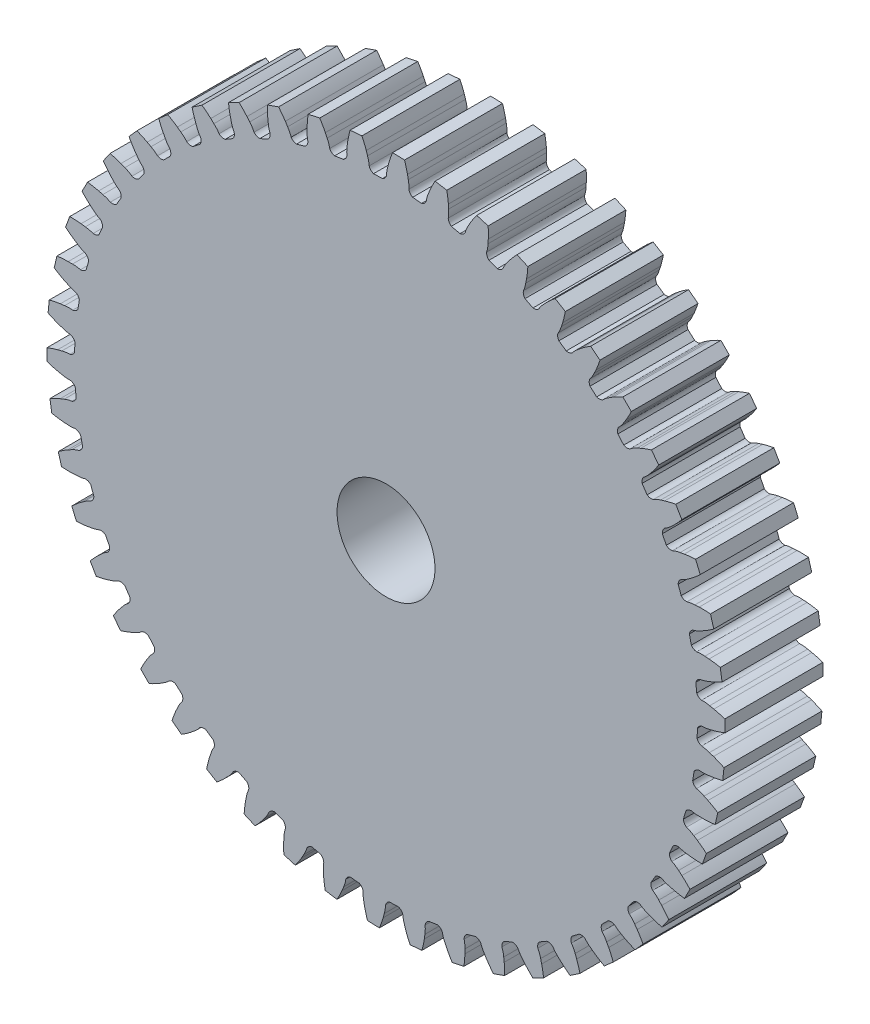
SolidWorks part; units mm, degrees
material "Alloy Steel"
ref_plane "Front Plane" through (0, 0, 0) normal (0, 0, 1) x (1, 0, 0)
ref_plane "Top Plane" through (0, 0, 0) normal (0, 1, 0) x (1, 0, 0)
ref_plane "Right Plane" through (0, 0, 0) normal (1, 0, 0) x (0, 0, -1)
ref_plane "Plane1" through (0, 0, 1.5875) normal (0, 0, 1) x (1, 0, 0)
sketch "Sketch1" plane through (0, 0, 1.5875) normal (0, 0, 1) x (1, 0, 0)
  line L0 (6.0854, 30.9194) -> (6.0622, 31.3363)
  line L1 (5.9106, 32.4269) -> (4.7682, 32.6145)
  line L2 (4.2758, 31.6296) -> (4.1205, 31.242)
  line L3 (3.4517, 30.0832) -> (2.5877, 30.1698)
  line L4 (2.1622, 31.4383) -> (2.087, 31.849)
  line L5 (1.7998, 32.912) -> (0.6429, 32.9549)
  line L6 (0.2778, 31.9161) -> (0.1724, 31.5121)
  line L7 (-0.3459, 30.2786) -> (-1.214, 30.2563)
  line L8 (-1.7951, 31.4614) -> (-1.9212, 31.8594)
  line L9 (-2.3393, 32.8781) -> (-3.4925, 32.7757)
  line L10 (-3.7245, 31.6992) -> (-3.7785, 31.2852)
  line L11 (-4.1381, 29.9965) -> (-4.9965, 29.8655)
  line L12 (-5.7241, 30.9883) -> (-5.8991, 31.3674)
  line L13 (-6.4416, 32.3256) -> (-7.5728, 32.0795)
  line L14 (-7.6681, 30.9825) -> (-7.6698, 30.5649)
  line L15 (-7.865, 29.2413) -> (-8.7003, 29.0038)
  line L16 (-9.5628, 30.0266) -> (-9.784, 30.3807)
  line L17 (-10.4423, 31.2634) -> (-11.5337, 30.8774)
  line L18 (-11.4908, 29.7771) -> (-11.4401, 29.3626)
  line L19 (-11.4679, 28.025) -> (-12.2668, 27.6847)
  line L20 (-13.2507, 28.5912) -> (-13.5145, 28.9149)
  line L21 (-14.2783, 29.7081) -> (-15.3128, 29.1884)
  line L22 (-15.1322, 28.1021) -> (-15.03, 27.6973)
  line L23 (-14.89, 26.3667) -> (-15.6399, 25.9289)
  line L24 (-16.7297, 26.705) -> (-17.032, 26.9931)
  line L25 (-17.8891, 27.6843) -> (-18.8503, 27.039)
  line L26 (-18.535, 25.9839) -> (-18.3829, 25.5951)
  line L27 (-18.0772, 24.2926) -> (-18.7663, 23.7643)
  line L28 (-19.9448, 24.3977) -> (-20.2808, 24.6455)
  line L29 (-21.2178, 25.2239) -> (-22.0905, 24.4632)
  line L30 (-21.6455, 23.456) -> (-21.4459, 23.0893)
  line L31 (-20.9793, 21.8354) -> (-21.5968, 21.2249)
  line L32 (-22.8454, 21.7055) -> (-23.2098, 21.9093)
  line L33 (-24.2119, 22.3657) -> (-24.9824, 21.5017)
  line L34 (-24.4147, 20.5581) -> (-24.1706, 20.2194)
  line L35 (-23.5506, 19.0338) -> (-24.0867, 18.3507)
  line L36 (-25.3856, 18.6711) -> (-25.7727, 18.8276)
  line L37 (-26.8242, 19.1548) -> (-27.4803, 18.201)
  line L38 (-26.7988, 17.3361) -> (-26.5142, 17.0305)
  line L39 (-25.7505, 15.932) -> (-26.1967, 15.1871)
  line L40 (-27.5256, 15.3422) -> (-27.9292, 15.449)
  line L41 (-29.0134, 15.6418) -> (-29.5448, 14.6133)
  line L42 (-28.7602, 13.8406) -> (-28.4396, 13.5731)
  line L43 (-27.5442, 12.579) -> (-27.8936, 11.7841)
  line L44 (-29.2314, 11.7714) -> (-29.6453, 11.8267)
  line L45 (-30.745, 11.8821) -> (-31.1433, 10.7951)
  line L46 (-30.2681, 10.1268) -> (-29.9165, 9.9017)
  line L47 (-28.9036, 9.0276) -> (-29.1506, 8.1951)
  line L48 (-30.4763, 8.0149) -> (-30.8938, 8.0179)
  line L49 (-31.9918, 7.935) -> (-32.2507, 6.8067)
  line L50 (-31.2987, 6.2534) -> (-30.9216, 6.0741)
  line L51 (-29.8071, 5.3339) -> (-29.9478, 4.477)
  line L52 (-31.2405, 4.132) -> (-31.6551, 4.0827)
  line L53 (-32.7341, 3.8628) -> (-32.8495, 2.7109)
  line L54 (-31.8356, 2.2813) -> (-31.4391, 2.1507)
  line L55 (-30.2406, 1.556) -> (-30.2728, 0.6882)
  line L56 (-31.512, 0.1839) -> (-31.9172, 0.083)
  line L57 (-32.9601, -0.2703) -> (-32.9303, -1.4276)
  line L58 (-31.8705, -1.7267) -> (-31.4607, -1.8066)
  line L59 (-30.1972, -2.2465) -> (-30.1203, -3.1114)
  line L60 (-31.2866, -3.767) -> (-31.6759, -3.9179)
  line L61 (-32.6663, -4.3992) -> (-32.4917, -5.5436)
  line L62 (-31.4028, -5.7076) -> (-30.9862, -5.7355)
  line L63 (-29.6775, -6.0134) -> (-29.4929, -6.8619)
  line L64 (-30.5678, -7.6586) -> (-30.9351, -7.8571)
  line L65 (-31.8574, -8.4586) -> (-31.5407, -9.5722)
  line L66 (-30.4398, -9.5984) -> (-30.023, -9.5738)
  line L67 (-28.6898, -9.6856) -> (-28.4003, -10.5043)
  line L68 (-29.3668, -11.4293) -> (-29.7064, -11.6723)
  line L69 (-30.546, -12.3847) -> (-30.0923, -13.4498)
  line L70 (-28.9968, -13.3378) -> (-28.5864, -13.2612)
  line L71 (-27.2496, -13.205) -> (-26.8598, -13.9809)
  line L72 (-27.7028, -15.0199) -> (-28.0092, -15.3034)
  line L73 (-28.7529, -16.1155) -> (-28.1693, -17.1153)
  line L74 (-27.0965, -16.8669) -> (-26.6989, -16.7395)
  line L75 (-25.3797, -16.5162) -> (-24.8957, -17.2371)
  line L76 (-25.6019, -18.3735) -> (-25.8703, -18.6933)
  line L77 (-26.5064, -19.5921) -> (-25.802, -20.5109)
  line L78 (-24.7688, -20.13) -> (-24.3903, -19.9538)
  line L79 (-23.1096, -19.5669) -> (-22.539, -20.2214)
  line L80 (-23.0972, -21.4374) -> (-23.3235, -21.7883)
  line L81 (-23.8418, -22.7598) -> (-23.0279, -23.583)
  line L82 (-22.0506, -23.0756) -> (-21.6972, -22.8533)
  line L83 (-20.475, -22.309) -> (-19.8269, -22.8869)
  line L84 (-20.2282, -24.1632) -> (-20.4088, -24.5397)
  line L85 (-20.8013, -25.5685) -> (-19.8906, -26.2832)
  line L86 (-18.9846, -25.6573) -> (-18.6618, -25.3925)
  line L87 (-17.5175, -24.6993) -> (-16.8021, -25.1914)
  line L88 (-17.0403, -26.5079) -> (-17.1722, -26.9041)
  line L89 (-17.4327, -27.974) -> (-16.4396, -28.5689)
  line L90 (-15.6191, -27.8344) -> (-15.3321, -27.5312)
  line L91 (-14.2837, -26.7) -> (-13.5123, -27.0986)
  line L92 (-13.5836, -28.4346) -> (-13.6648, -28.8442)
  line L93 (-13.7892, -29.9383) -> (-12.7293, -30.404)
  line L94 (-12.0074, -29.5725) -> (-11.7606, -29.2357)
  line L95 (-10.8247, -28.2797) -> (-10.0094, -28.5785)
  line L96 (-9.9127, -29.9129) -> (-9.9419, -30.3294)
  line L97 (-9.9282, -31.4304) -> (-8.8183, -31.7597)
  line L98 (-8.2063, -30.8443) -> (-8.0037, -30.4792)
  line L99 (-7.1949, -29.4134) -> (-6.3486, -29.6076)
  line L100 (-6.0854, -30.9194) -> (-6.0622, -31.3363)
  line L101 (-5.9106, -32.4269) -> (-4.7682, -32.6145)
  line L102 (-4.2758, -31.6296) -> (-4.1205, -31.242)
  line L103 (-3.4517, -30.0832) -> (-2.5877, -30.1698)
  line L104 (-2.1622, -31.4383) -> (-2.087, -31.849)
  line L105 (-1.7998, -32.912) -> (-0.6429, -32.9549)
  line L106 (-0.2778, -31.9161) -> (-0.1724, -31.5121)
  line L107 (0.3459, -30.2786) -> (1.214, -30.2563)
  line L108 (1.7951, -31.4614) -> (1.9212, -31.8594)
  line L109 (2.3393, -32.8781) -> (3.4925, -32.7757)
  line L110 (3.7245, -31.6992) -> (3.7785, -31.2852)
  line L111 (4.1381, -29.9965) -> (4.9965, -29.8655)
  line L112 (5.7241, -30.9883) -> (5.8991, -31.3674)
  line L113 (6.4416, -32.3256) -> (7.5728, -32.0795)
  line L114 (7.6681, -30.9825) -> (7.6698, -30.5649)
  line L115 (7.865, -29.2413) -> (8.7003, -29.0038)
  line L116 (9.5628, -30.0266) -> (9.784, -30.3807)
  line L117 (10.4423, -31.2634) -> (11.5337, -30.8774)
  line L118 (11.4908, -29.7771) -> (11.4401, -29.3626)
  line L119 (11.4679, -28.025) -> (12.2668, -27.6847)
  line L120 (13.2507, -28.5912) -> (13.5145, -28.9149)
  line L121 (14.2783, -29.7081) -> (15.3128, -29.1884)
  line L122 (15.1322, -28.1021) -> (15.03, -27.6973)
  line L123 (14.89, -26.3667) -> (15.6399, -25.9289)
  line L124 (16.7297, -26.705) -> (17.032, -26.9931)
  line L125 (17.8891, -27.6843) -> (18.8503, -27.039)
  line L126 (18.535, -25.9839) -> (18.3829, -25.5951)
  line L127 (18.0772, -24.2926) -> (18.7663, -23.7643)
  line L128 (19.9448, -24.3977) -> (20.2808, -24.6455)
  line L129 (21.2178, -25.2239) -> (22.0905, -24.4632)
  line L130 (21.6455, -23.456) -> (21.4459, -23.0893)
  line L131 (20.9793, -21.8354) -> (21.5968, -21.2249)
  line L132 (22.8454, -21.7055) -> (23.2098, -21.9093)
  line L133 (24.2119, -22.3657) -> (24.9824, -21.5017)
  line L134 (24.4147, -20.5581) -> (24.1706, -20.2194)
  line L135 (23.5506, -19.0338) -> (24.0867, -18.3507)
  line L136 (25.3856, -18.6711) -> (25.7727, -18.8276)
  line L137 (26.8242, -19.1548) -> (27.4803, -18.201)
  line L138 (26.7988, -17.3361) -> (26.5142, -17.0305)
  line L139 (25.7505, -15.932) -> (26.1967, -15.1871)
  line L140 (27.5256, -15.3422) -> (27.9292, -15.449)
  line L141 (29.0134, -15.6418) -> (29.5448, -14.6133)
  line L142 (28.7602, -13.8406) -> (28.4396, -13.5731)
  line L143 (27.5442, -12.579) -> (27.8936, -11.7841)
  line L144 (29.2314, -11.7714) -> (29.6453, -11.8267)
  line L145 (30.745, -11.8821) -> (31.1433, -10.7951)
  line L146 (30.2681, -10.1268) -> (29.9165, -9.9017)
  line L147 (28.9036, -9.0276) -> (29.1506, -8.1951)
  line L148 (30.4763, -8.0149) -> (30.8938, -8.0179)
  line L149 (31.9918, -7.935) -> (32.2507, -6.8067)
  line L150 (31.2987, -6.2534) -> (30.9216, -6.0741)
  line L151 (29.8071, -5.3339) -> (29.9478, -4.477)
  line L152 (31.2405, -4.132) -> (31.6551, -4.0827)
  line L153 (32.7341, -3.8628) -> (32.8495, -2.7109)
  line L154 (31.8356, -2.2813) -> (31.4391, -2.1507)
  line L155 (30.2406, -1.556) -> (30.2728, -0.6882)
  line L156 (31.512, -0.1839) -> (31.9172, -0.083)
  line L157 (32.9601, 0.2703) -> (32.9303, 1.4276)
  line L158 (31.8705, 1.7267) -> (31.4607, 1.8066)
  line L159 (30.1972, 2.2465) -> (30.1203, 3.1114)
  line L160 (31.2866, 3.767) -> (31.6759, 3.9179)
  line L161 (32.6663, 4.3992) -> (32.4917, 5.5436)
  line L162 (31.4028, 5.7076) -> (30.9862, 5.7355)
  line L163 (29.6775, 6.0134) -> (29.4929, 6.8619)
  line L164 (30.5678, 7.6586) -> (30.9351, 7.8571)
  line L165 (31.8574, 8.4586) -> (31.5407, 9.5722)
  line L166 (30.4398, 9.5984) -> (30.023, 9.5738)
  line L167 (28.6898, 9.6856) -> (28.4003, 10.5043)
  line L168 (29.3668, 11.4293) -> (29.7064, 11.6723)
  line L169 (30.546, 12.3847) -> (30.0923, 13.4498)
  line L170 (28.9968, 13.3378) -> (28.5864, 13.2612)
  line L171 (27.2496, 13.205) -> (26.8598, 13.9809)
  line L172 (27.7028, 15.0199) -> (28.0092, 15.3034)
  line L173 (28.7529, 16.1155) -> (28.1693, 17.1153)
  line L174 (27.0965, 16.8669) -> (26.6989, 16.7395)
  line L175 (25.3797, 16.5162) -> (24.8957, 17.2371)
  line L176 (25.6019, 18.3735) -> (25.8703, 18.6933)
  line L177 (26.5064, 19.5921) -> (25.802, 20.5109)
  line L178 (24.7688, 20.13) -> (24.3903, 19.9538)
  line L179 (23.1096, 19.5669) -> (22.539, 20.2214)
  line L180 (23.0972, 21.4374) -> (23.3235, 21.7883)
  line L181 (23.8418, 22.7598) -> (23.0279, 23.583)
  line L182 (22.0506, 23.0756) -> (21.6972, 22.8533)
  line L183 (20.475, 22.309) -> (19.8269, 22.8869)
  line L184 (20.2282, 24.1632) -> (20.4088, 24.5397)
  line L185 (20.8013, 25.5685) -> (19.8906, 26.2832)
  line L186 (18.9846, 25.6573) -> (18.6618, 25.3925)
  line L187 (17.5175, 24.6993) -> (16.8021, 25.1914)
  line L188 (17.0403, 26.5079) -> (17.1722, 26.9041)
  line L189 (17.4327, 27.974) -> (16.4396, 28.5689)
  line L190 (15.6191, 27.8344) -> (15.3321, 27.5312)
  line L191 (14.2837, 26.7) -> (13.5123, 27.0986)
  line L192 (13.5836, 28.4346) -> (13.6648, 28.8442)
  line L193 (13.7892, 29.9383) -> (12.7293, 30.404)
  line L194 (12.0074, 29.5725) -> (11.7606, 29.2357)
  line L195 (10.8247, 28.2797) -> (10.0094, 28.5785)
  line L196 (9.9127, 29.9129) -> (9.9419, 30.3294)
  line L197 (9.9282, 31.4304) -> (8.8183, 31.7597)
  line L198 (8.2063, 30.8443) -> (8.0037, 30.4792)
  line L199 (7.1949, 29.4134) -> (6.3486, 29.6076)
  circle A0 centre (0, 0) radius 4.7625
  arc A1 (6.3486, 29.6076) -> (6.0483, 30.1378) centre (6.7187, 30.1674) cw
  arc A2 (6.0483, 30.1378) -> (6.0854, 30.9194) centre (3.3661, 30.657) ccw
  arc A3 (6.0622, 31.3363) -> (5.9106, 32.4269) centre (-4.1695, 30.4695) ccw
  arc A4 (4.7682, 32.6145) -> (4.2758, 31.6296) centre (13.6932, 27.5367) ccw
  arc A5 (4.1205, 31.242) -> (3.9058, 30.4895) centre (6.6132, 30.1239) ccw
  arc A6 (3.9058, 30.4895) -> (3.4517, 30.0832) centre (3.2801, 30.732) cw
  arc A7 (2.5877, 30.1698) -> (2.2233, 30.6582) centre (2.8847, 30.7716) cw
  arc A8 (2.2233, 30.6582) -> (2.1622, 31.4383) centre (-0.5028, 30.8371) ccw
  arc A9 (2.087, 31.849) -> (1.7998, 32.912) centre (-7.9554, 29.7067) ccw
  arc A10 (0.6429, 32.9549) -> (0.2778, 31.9161) centre (10.1339, 29.0358) ccw
  arc A11 (0.1724, 31.5121) -> (0.0536, 30.7386) centre (2.7856, 30.7152) ccw
  arc A12 (0.0536, 30.7386) -> (-0.3459, 30.2786) centre (-0.5975, 30.9007) cw
  arc A13 (-1.214, 30.2563) -> (-1.6367, 30.6951) centre (-0.9947, 30.8905) cw
  arc A14 (-1.6367, 30.6951) -> (-1.7951, 31.4614) centre (-4.3638, 30.531) ccw
  arc A15 (-1.9212, 31.8594) -> (-2.3393, 32.8781) centre (-11.6159, 28.4753) ccw
  arc A16 (-3.4925, 32.7757) -> (-3.7245, 31.6992) centre (6.4149, 30.077) ccw
  arc A17 (-3.7785, 31.2852) -> (-3.7993, 30.503) centre (-1.086, 30.8221) ccw
  arc A18 (-3.7993, 30.503) -> (-4.1381, 29.9965) centre (-4.4657, 30.5822) cw
  arc A19 (-4.9965, 29.8655) -> (-5.4709, 30.2479) centre (-4.8585, 30.5223) cw
  arc A20 (-5.4709, 30.2479) -> (-5.7241, 30.9883) centre (-8.1559, 29.7433) ccw
  arc A21 (-5.8991, 31.3674) -> (-6.4416, 32.3256) centre (-15.0932, 26.7949) ccw
  arc A22 (-7.5728, 32.0795) -> (-7.6681, 30.9825) centre (2.5947, 30.6438) ccw
  arc A23 (-7.6698, 30.5649) -> (-7.5924, 29.7863) centre (-4.9405, 30.4429) ccw
  arc A24 (-7.5924, 29.7863) -> (-7.865, 29.2413) centre (-8.2635, 29.7813) cw
  arc A25 (-8.7003, 29.0038) -> (-9.2188, 29.3237) centre (-8.6456, 29.6726) cw
  arc A26 (-9.2188, 29.3237) -> (-9.5628, 30.0266) centre (-11.8194, 28.4865) ccw
  arc A27 (-9.784, 30.3807) -> (-10.4423, 31.2634) centre (-18.3325, 24.692) ccw
  arc A28 (-11.5337, 30.8774) -> (-11.4908, 29.7771) centre (-1.2665, 30.7274) ccw
  arc A29 (-11.4401, 29.3626) -> (-11.2658, 28.5998) centre (-8.7171, 29.5837) ccw
  arc A30 (-11.2658, 28.5998) -> (-11.4679, 28.025) centre (-11.9309, 28.5108) cw
  arc A31 (-12.2668, 27.6847) -> (-12.8214, 27.9371) centre (-12.2964, 28.3551) cw
  arc A32 (-12.8214, 27.9371) -> (-13.2507, 28.5912) centre (-15.2965, 26.7805) ccw
  arc A33 (-13.5145, 28.9149) -> (-14.2783, 29.7081) centre (-21.2827, 22.1996) ccw
  arc A34 (-15.3128, 29.1884) -> (-15.1322, 28.1021) centre (-5.1077, 30.3263) ccw
  arc A35 (-15.03, 27.6973) -> (-14.7614, 26.9623) centre (-12.3561, 28.2579) ccw
  arc A36 (-14.7614, 26.9623) -> (-14.89, 26.3667) centre (-15.4102, 26.7907) cw
  arc A37 (-15.6399, 25.9289) -> (-16.2217, 26.1098) centre (-15.7533, 26.5903) cw
  arc A38 (-16.2217, 26.1098) -> (-16.7297, 26.705) centre (-18.5324, 24.6522) ccw
  arc A39 (-17.032, 26.9931) -> (-17.8891, 27.6843) centre (-23.8972, 19.3571) ccw
  arc A40 (-18.8503, 27.039) -> (-18.535, 25.9839) centre (-8.8683, 29.447) ccw
  arc A41 (-18.3829, 25.5951) -> (-18.0243, 24.8996) centre (-15.8004, 26.4864) ccw
  arc A42 (-18.0243, 24.8996) -> (-18.0772, 24.2926) centre (-18.6464, 24.648) cw
  arc A43 (-18.7663, 23.7643) -> (-19.3662, 23.8708) centre (-18.9617, 24.4063) cw
  arc A44 (-19.3662, 23.8708) -> (-19.9448, 24.3977) centre (-21.476, 22.1351) ccw
  arc A45 (-20.2808, 24.6455) -> (-21.2178, 25.2239) centre (-26.1349, 16.2094) ccw
  arc A46 (-22.0905, 24.4632) -> (-21.6455, 23.456) centre (-12.489, 28.1033) ccw
  arc A47 (-21.4459, 23.0893) -> (-21.0029, 22.4442) centre (-18.9954, 24.2972) ccw
  arc A48 (-21.0029, 22.4442) -> (-20.9793, 21.8354) centre (-21.5886, 22.1166) cw
  arc A49 (-21.5968, 21.2249) -> (-22.2053, 21.2554) centre (-21.8711, 21.8373) cw
  arc A50 (-22.2053, 21.2554) -> (-22.8454, 21.7055) centre (-24.0809, 19.2689) ccw
  arc A51 (-23.2098, 21.9093) -> (-24.2119, 22.3657) centre (-27.9603, 12.806) ccw
  arc A52 (-24.9824, 21.5017) -> (-24.4147, 20.5581) centre (-15.9128, 26.3165) ccw
  arc A53 (-24.1706, 20.2194) -> (-23.6503, 19.6349) centre (-21.8909, 21.7249) ccw
  arc A54 (-23.6503, 19.6349) -> (-23.5506, 19.0338) centre (-24.1903, 19.2365) cw
  arc A55 (-24.0867, 18.3507) -> (-24.6942, 18.3047) centre (-24.4356, 18.9239) cw
  arc A56 (-24.6942, 18.3047) -> (-25.3856, 18.6711) centre (-26.3061, 16.0988) ccw
  arc A57 (-25.7727, 18.8276) -> (-26.8242, 19.1548) centre (-29.3449, 9.2006) ccw
  arc A58 (-27.4803, 18.201) -> (-26.7988, 17.3361) centre (-19.0857, 24.1145) ccw
  arc A59 (-26.5142, 17.0305) -> (-25.9247, 16.5159) centre (-24.4411, 18.8099) ccw
  arc A60 (-25.9247, 16.5159) -> (-25.7505, 15.932) centre (-26.4105, 16.0529) cw
  arc A61 (-26.1967, 15.1871) -> (-26.7937, 15.0653) centre (-26.6147, 15.7121) cw
  arc A62 (-26.7937, 15.0653) -> (-27.5256, 15.3422) centre (-28.1164, 12.6748) ccw
  arc A63 (-27.9292, 15.449) -> (-29.0134, 15.6418) centre (-30.2666, 5.4502) ccw
  arc A64 (-29.5448, 14.6133) -> (-28.7602, 13.8406) centre (-21.9575, 21.5323) ccw
  arc A65 (-28.4396, 13.5731) -> (-27.7903, 13.1364) centre (-26.6059, 15.5983) ccw
  arc A66 (-27.7903, 13.1364) -> (-27.5442, 12.579) centre (-28.2142, 12.6162) cw
  arc A67 (-27.8936, 11.7841) -> (-28.4706, 11.5884) centre (-28.3741, 12.2525) cw
  arc A68 (-28.4706, 11.5884) -> (-29.2314, 11.7714) centre (-29.4832, 9.051) ccw
  arc A69 (-29.6453, 11.8267) -> (-30.745, 11.8821) centre (-30.7111, 1.6138) ccw
  arc A70 (-31.1433, 10.7951) -> (-30.2681, 10.1268) centre (-24.4831, 18.6105) ccw
  arc A71 (-29.9165, 9.9017) -> (-29.2176, 9.5498) centre (-28.3511, 12.1407) ccw
  arc A72 (-29.2176, 9.5498) -> (-28.9036, 9.0276) centre (-29.573, 8.9806) cw
  arc A73 (-29.1506, 8.1951) -> (-29.6985, 7.9287) centre (-29.686, 8.5997) cw
  arc A74 (-29.6985, 7.9287) -> (-30.4763, 8.0149) centre (-30.3851, 5.2844) ccw
  arc A75 (-30.8938, 8.0179) -> (-31.9918, 7.935) centre (-30.6712, -2.248) ccw
  arc A76 (-32.2507, 6.8067) -> (-31.2987, 6.2534) centre (-26.6226, 15.3952) ccw
  arc A77 (-30.9216, 6.0741) -> (-30.1841, 5.8125) centre (-29.6492, 8.4917) ccw
  arc A78 (-30.1841, 5.8125) -> (-29.8071, 5.3339) centre (-30.4654, 5.2033) cw
  arc A79 (-29.9478, 4.477) -> (-30.4581, 4.144) centre (-30.5297, 4.8112) cw
  arc A80 (-30.4581, 4.144) -> (-31.2405, 4.132) centre (-30.8079, 1.4344) ccw
  arc A81 (-31.6551, 4.0827) -> (-32.7341, 3.8628) centre (-30.1476, -6.0744) ccw
  arc A82 (-32.8495, 2.7109) -> (-31.8356, 2.2813) centre (-28.3422, 11.9371) ccw
  arc A83 (-31.4391, 2.1507) -> (-30.6746, 1.9836) centre (-30.4797, 4.7087) ccw
  arc A84 (-30.6746, 1.9836) -> (-30.2406, 1.556) centre (-30.8773, 1.3439) cw
  arc A85 (-30.2728, 0.6882) -> (-30.7373, 0.2939) centre (-30.892, 0.9469) cw
  arc A86 (-30.7373, 0.2939) -> (-31.512, 0.1839) centre (-30.7447, -2.4381) ccw
  arc A87 (-31.9172, 0.083) -> (-32.9601, -0.2703) centre (-29.1485, -9.805) ccw
  arc A88 (-32.9303, -1.4276) -> (-31.8705, -1.7267) centre (-29.6148, 8.2908) ccw
  arc A89 (-31.4607, -1.8066) -> (-30.6814, -1.8766) centre (-30.8295, 0.8514) ccw
  arc A90 (-30.6814, -1.8766) -> (-30.1972, -2.2465) centre (-30.8022, -2.5366) cw
  arc A91 (-30.1203, -3.1114) -> (-30.5317, -3.5608) centre (-30.7671, -2.9324) cw
  arc A92 (-30.5317, -3.5608) -> (-31.2866, -3.767) centre (-30.1967, -6.2722) ccw
  arc A93 (-31.6759, -3.9179) -> (-32.6663, -4.3992) centre (-27.6898, -13.381) ccw
  arc A94 (-32.4917, -5.5436) -> (-31.4028, -5.7076) centre (-30.4204, 4.5137) ccw
  arc A95 (-30.9862, -5.7355) -> (-30.2042, -5.7071) centre (-30.6931, -3.0192) ccw
  arc A96 (-30.2042, -5.7071) -> (-29.6775, -6.0134) centre (-30.2414, -6.3772) cw
  arc A97 (-29.4929, -6.8619) -> (-29.8447, -7.3594) centre (-30.157, -6.7654) cw
  arc A98 (-29.8447, -7.3594) -> (-30.5678, -7.6586) centre (-29.1725, -10.0074) ccw
  arc A99 (-30.9351, -7.8571) -> (-31.8574, -8.4586) centre (-25.7944, -16.7459) ccw
  arc A100 (-31.5407, -9.5722) -> (-30.4398, -9.5984) centre (-30.7462, 0.6654) ccw
  arc A101 (-30.023, -9.5738) -> (-29.2508, -9.4477) centre (-30.0727, -6.8423) ccw
  arc A102 (-29.2508, -9.4477) -> (-28.6898, -9.6856) centre (-29.2037, -10.1172) cw
  arc A103 (-28.4003, -10.5043) -> (-28.687, -11.0419) centre (-29.0712, -10.4917) cw
  arc A104 (-28.687, -11.0419) -> (-29.3668, -11.4293) centre (-27.6882, -13.5848) ccw
  arc A105 (-29.7064, -11.6723) -> (-30.546, -12.3847) centre (-23.4921, -19.8468) ccw
  arc A106 (-30.0923, -13.4498) -> (-28.9968, -13.3378) centre (-30.5872, -3.1934) ccw
  arc A107 (-28.5864, -13.2612) -> (-27.836, -13.0393) centre (-28.978, -10.5574) ccw
  arc A108 (-27.836, -13.0393) -> (-27.2496, -13.205) centre (-27.7054, -13.6976) cw
  arc A109 (-26.8598, -13.9809) -> (-27.0769, -14.5503) centre (-27.527, -14.0526) cw
  arc A110 (-27.0769, -14.5503) -> (-27.7028, -15.0199) centre (-25.7672, -16.9479) ccw
  arc A111 (-28.0092, -15.3034) -> (-28.7529, -16.1155) centre (-20.8194, -22.6346) ccw
  arc A112 (-28.1693, -17.1153) -> (-27.0965, -16.8669) centre (-29.9458, -7.0018) ccw
  arc A113 (-26.6989, -16.7395) -> (-25.9822, -16.4253) centre (-27.4263, -14.1061) ccw
  arc A114 (-25.9822, -16.4253) -> (-25.3797, -16.5162) centre (-25.7702, -17.062) cw
  arc A115 (-24.8957, -17.2371) -> (-25.0397, -17.8292) centre (-25.5487, -17.3918) cw
  arc A116 (-25.0397, -17.8292) -> (-25.6019, -18.3735) centre (-23.4399, -20.0438) ccw
  arc A117 (-25.8703, -18.6933) -> (-26.5064, -19.5921) centre (-17.8184, -25.0655) ccw
  arc A118 (-25.802, -20.5109) -> (-24.7688, -20.13) centre (-28.8321, -10.6998) ccw
  arc A119 (-24.3903, -19.9538) -> (-23.7187, -19.5522) centre (-25.442, -17.4323) ccw
  arc A120 (-23.7187, -19.5522) -> (-23.1096, -19.5669) centre (-23.4285, -20.1573) cw
  arc A121 (-22.539, -20.2214) -> (-22.6077, -20.8269) centre (-23.1675, -20.4568) cw
  arc A122 (-22.6077, -20.8269) -> (-23.0972, -21.4374) centre (-20.7429, -22.8235) ccw
  arc A123 (-23.3235, -21.7883) -> (-23.8418, -22.7598) centre (-14.5364, -27.1011) ccw
  arc A124 (-23.0279, -23.583) -> (-22.0506, -23.0756) centre (-27.2637, -14.229) ccw
  arc A125 (-21.6972, -22.8533) -> (-21.0812, -22.3708) centre (-23.0566, -20.4836) ccw
  arc A126 (-21.0812, -22.3708) -> (-20.475, -22.309) centre (-20.7174, -22.9347) cw
  arc A127 (-19.8269, -22.8869) -> (-19.8191, -23.4962) centre (-20.4209, -23.1991) cw
  arc A128 (-19.8191, -23.4962) -> (-20.2282, -24.1632) centre (-17.7188, -25.2433) ccw
  arc A129 (-20.4088, -24.5397) -> (-20.8013, -25.5685) centre (-11.0251, -28.7093) ccw
  arc A130 (-19.8906, -26.2832) -> (-18.9846, -25.6573) centre (-25.2653, -17.5339) ccw
  arc A131 (-18.6618, -25.3925) -> (-18.1111, -24.8365) centre (-20.3075, -23.2118) ccw
  arc A132 (-18.1111, -24.8365) -> (-17.5175, -24.6993) centre (-17.6796, -25.3505) cw
  arc A133 (-16.8021, -25.1914) -> (-16.718, -25.7949) centre (-17.3522, -25.5756) cw
  arc A134 (-16.718, -25.7949) -> (-17.0403, -26.5079) centre (-14.4153, -27.265) ccw
  arc A135 (-17.1722, -26.9041) -> (-17.4327, -27.974) centre (-7.3399, -29.8647) ccw
  arc A136 (-16.4396, -28.5689) -> (-15.6191, -27.8344) centre (-22.8685, -20.5622) ccw
  arc A137 (-15.3321, -27.5312) -> (-14.8555, -26.9106) centre (-17.2382, -25.574) ccw
  arc A138 (-14.8555, -26.9106) -> (-14.2837, -26.7) centre (-14.3629, -27.3664) cw
  arc A139 (-13.5123, -27.0986) -> (-13.3532, -27.6868) centre (-14.0099, -27.5488) cw
  arc A140 (-13.3532, -27.6868) -> (-13.5836, -28.4346) centre (-10.8844, -28.8567) ccw
  arc A141 (-13.6648, -28.8442) -> (-13.7892, -29.9383) centre (-3.539, -30.5491) ccw
  arc A142 (-12.7293, -30.404) -> (-12.0074, -29.5725) centre (-20.1111, -23.2662) ccw
  arc A143 (-11.7606, -29.2357) -> (-11.3655, -28.5603) centre (-13.897, -27.5328) ccw
  arc A144 (-11.3655, -28.5603) -> (-10.8247, -28.2797) centre (-10.8197, -28.9508) cw
  arc A145 (-10.0094, -28.5785) -> (-9.7778, -29.1421) centre (-10.4467, -29.0874) cw
  arc A146 (-9.7778, -29.1421) -> (-9.9127, -29.9129) centre (-7.1819, -29.9934) ccw
  arc A147 (-9.9419, -30.3294) -> (-9.9282, -31.4304) centre (0.3177, -30.7518) ccw
  arc A148 (-8.8183, -31.7597) -> (-8.2063, -30.8443) centre (-17.0365, -25.6034) ccw
  arc A149 (-8.0037, -30.4792) -> (-7.6964, -29.7596) centre (-10.3366, -29.0575) ccw
  arc A150 (-7.6964, -29.7596) -> (-7.1949, -29.4134) centre (-7.1059, -30.0785) cw
  arc A151 (-6.3486, -29.6076) -> (-6.0483, -30.1378) centre (-6.7187, -30.1674) cw
  arc A152 (-6.0483, -30.1378) -> (-6.0854, -30.9194) centre (-3.3661, -30.657) ccw
  arc A153 (-6.0622, -31.3363) -> (-5.9106, -32.4269) centre (4.1695, -30.4695) ccw
  arc A154 (-4.7682, -32.6145) -> (-4.2758, -31.6296) centre (-13.6932, -27.5367) ccw
  arc A155 (-4.1205, -31.242) -> (-3.9058, -30.4895) centre (-6.6132, -30.1239) ccw
  arc A156 (-3.9058, -30.4895) -> (-3.4517, -30.0832) centre (-3.2801, -30.732) cw
  arc A157 (-2.5877, -30.1698) -> (-2.2233, -30.6582) centre (-2.8847, -30.7716) cw
  arc A158 (-2.2233, -30.6582) -> (-2.1622, -31.4383) centre (0.5028, -30.8371) ccw
  arc A159 (-2.087, -31.849) -> (-1.7998, -32.912) centre (7.9554, -29.7067) ccw
  arc A160 (-0.6429, -32.9549) -> (-0.2778, -31.9161) centre (-10.1339, -29.0358) ccw
  arc A161 (-0.1724, -31.5121) -> (-0.0536, -30.7386) centre (-2.7856, -30.7152) ccw
  arc A162 (-0.0536, -30.7386) -> (0.3459, -30.2786) centre (0.5975, -30.9007) cw
  arc A163 (1.214, -30.2563) -> (1.6367, -30.6951) centre (0.9947, -30.8905) cw
  arc A164 (1.6367, -30.6951) -> (1.7951, -31.4614) centre (4.3638, -30.531) ccw
  arc A165 (1.9212, -31.8594) -> (2.3393, -32.8781) centre (11.6159, -28.4753) ccw
  arc A166 (3.4925, -32.7757) -> (3.7245, -31.6992) centre (-6.4149, -30.077) ccw
  arc A167 (3.7785, -31.2852) -> (3.7993, -30.503) centre (1.086, -30.8221) ccw
  arc A168 (3.7993, -30.503) -> (4.1381, -29.9965) centre (4.4657, -30.5822) cw
  arc A169 (4.9965, -29.8655) -> (5.4709, -30.2479) centre (4.8585, -30.5223) cw
  arc A170 (5.4709, -30.2479) -> (5.7241, -30.9883) centre (8.1559, -29.7433) ccw
  arc A171 (5.8991, -31.3674) -> (6.4416, -32.3256) centre (15.0932, -26.7949) ccw
  arc A172 (7.5728, -32.0795) -> (7.6681, -30.9825) centre (-2.5947, -30.6438) ccw
  arc A173 (7.6698, -30.5649) -> (7.5924, -29.7863) centre (4.9405, -30.4429) ccw
  arc A174 (7.5924, -29.7863) -> (7.865, -29.2413) centre (8.2635, -29.7813) cw
  arc A175 (8.7003, -29.0038) -> (9.2188, -29.3237) centre (8.6456, -29.6726) cw
  arc A176 (9.2188, -29.3237) -> (9.5628, -30.0266) centre (11.8194, -28.4865) ccw
  arc A177 (9.784, -30.3807) -> (10.4423, -31.2634) centre (18.3325, -24.692) ccw
  arc A178 (11.5337, -30.8774) -> (11.4908, -29.7771) centre (1.2665, -30.7274) ccw
  arc A179 (11.4401, -29.3626) -> (11.2658, -28.5998) centre (8.7171, -29.5837) ccw
  arc A180 (11.2658, -28.5998) -> (11.4679, -28.025) centre (11.9309, -28.5108) cw
  arc A181 (12.2668, -27.6847) -> (12.8214, -27.9371) centre (12.2964, -28.3551) cw
  arc A182 (12.8214, -27.9371) -> (13.2507, -28.5912) centre (15.2965, -26.7805) ccw
  arc A183 (13.5145, -28.9149) -> (14.2783, -29.7081) centre (21.2827, -22.1996) ccw
  arc A184 (15.3128, -29.1884) -> (15.1322, -28.1021) centre (5.1077, -30.3263) ccw
  arc A185 (15.03, -27.6973) -> (14.7614, -26.9623) centre (12.3561, -28.2579) ccw
  arc A186 (14.7614, -26.9623) -> (14.89, -26.3667) centre (15.4102, -26.7907) cw
  arc A187 (15.6399, -25.9289) -> (16.2217, -26.1098) centre (15.7533, -26.5903) cw
  arc A188 (16.2217, -26.1098) -> (16.7297, -26.705) centre (18.5324, -24.6522) ccw
  arc A189 (17.032, -26.9931) -> (17.8891, -27.6843) centre (23.8972, -19.3571) ccw
  arc A190 (18.8503, -27.039) -> (18.535, -25.9839) centre (8.8683, -29.447) ccw
  arc A191 (18.3829, -25.5951) -> (18.0243, -24.8996) centre (15.8004, -26.4864) ccw
  arc A192 (18.0243, -24.8996) -> (18.0772, -24.2926) centre (18.6464, -24.648) cw
  arc A193 (18.7663, -23.7643) -> (19.3662, -23.8708) centre (18.9617, -24.4063) cw
  arc A194 (19.3662, -23.8708) -> (19.9448, -24.3977) centre (21.476, -22.1351) ccw
  arc A195 (20.2808, -24.6455) -> (21.2178, -25.2239) centre (26.1349, -16.2094) ccw
  arc A196 (22.0905, -24.4632) -> (21.6455, -23.456) centre (12.489, -28.1033) ccw
  arc A197 (21.4459, -23.0893) -> (21.0029, -22.4442) centre (18.9954, -24.2972) ccw
  arc A198 (21.0029, -22.4442) -> (20.9793, -21.8354) centre (21.5886, -22.1166) cw
  arc A199 (21.5968, -21.2249) -> (22.2053, -21.2554) centre (21.8711, -21.8373) cw
  arc A200 (22.2053, -21.2554) -> (22.8454, -21.7055) centre (24.0809, -19.2689) ccw
  arc A201 (23.2098, -21.9093) -> (24.2119, -22.3657) centre (27.9603, -12.806) ccw
  arc A202 (24.9824, -21.5017) -> (24.4147, -20.5581) centre (15.9128, -26.3165) ccw
  arc A203 (24.1706, -20.2194) -> (23.6503, -19.6349) centre (21.8909, -21.7249) ccw
  arc A204 (23.6503, -19.6349) -> (23.5506, -19.0338) centre (24.1903, -19.2365) cw
  arc A205 (24.0867, -18.3507) -> (24.6942, -18.3047) centre (24.4356, -18.9239) cw
  arc A206 (24.6942, -18.3047) -> (25.3856, -18.6711) centre (26.3061, -16.0988) ccw
  arc A207 (25.7727, -18.8276) -> (26.8242, -19.1548) centre (29.3449, -9.2006) ccw
  arc A208 (27.4803, -18.201) -> (26.7988, -17.3361) centre (19.0857, -24.1145) ccw
  arc A209 (26.5142, -17.0305) -> (25.9247, -16.5159) centre (24.4411, -18.8099) ccw
  arc A210 (25.9247, -16.5159) -> (25.7505, -15.932) centre (26.4105, -16.0529) cw
  arc A211 (26.1967, -15.1871) -> (26.7937, -15.0653) centre (26.6147, -15.7121) cw
  arc A212 (26.7937, -15.0653) -> (27.5256, -15.3422) centre (28.1164, -12.6748) ccw
  arc A213 (27.9292, -15.449) -> (29.0134, -15.6418) centre (30.2666, -5.4502) ccw
  arc A214 (29.5448, -14.6133) -> (28.7602, -13.8406) centre (21.9575, -21.5323) ccw
  arc A215 (28.4396, -13.5731) -> (27.7903, -13.1364) centre (26.6059, -15.5983) ccw
  arc A216 (27.7903, -13.1364) -> (27.5442, -12.579) centre (28.2142, -12.6162) cw
  arc A217 (27.8936, -11.7841) -> (28.4706, -11.5884) centre (28.3741, -12.2525) cw
  arc A218 (28.4706, -11.5884) -> (29.2314, -11.7714) centre (29.4832, -9.051) ccw
  arc A219 (29.6453, -11.8267) -> (30.745, -11.8821) centre (30.7111, -1.6138) ccw
  arc A220 (31.1433, -10.7951) -> (30.2681, -10.1268) centre (24.4831, -18.6105) ccw
  arc A221 (29.9165, -9.9017) -> (29.2176, -9.5498) centre (28.3511, -12.1407) ccw
  arc A222 (29.2176, -9.5498) -> (28.9036, -9.0276) centre (29.573, -8.9806) cw
  arc A223 (29.1506, -8.1951) -> (29.6985, -7.9287) centre (29.686, -8.5997) cw
  arc A224 (29.6985, -7.9287) -> (30.4763, -8.0149) centre (30.3851, -5.2844) ccw
  arc A225 (30.8938, -8.0179) -> (31.9918, -7.935) centre (30.6712, 2.248) ccw
  arc A226 (32.2507, -6.8067) -> (31.2987, -6.2534) centre (26.6226, -15.3952) ccw
  arc A227 (30.9216, -6.0741) -> (30.1841, -5.8125) centre (29.6492, -8.4917) ccw
  arc A228 (30.1841, -5.8125) -> (29.8071, -5.3339) centre (30.4654, -5.2033) cw
  arc A229 (29.9478, -4.477) -> (30.4581, -4.144) centre (30.5297, -4.8112) cw
  arc A230 (30.4581, -4.144) -> (31.2405, -4.132) centre (30.8079, -1.4344) ccw
  arc A231 (31.6551, -4.0827) -> (32.7341, -3.8628) centre (30.1476, 6.0744) ccw
  arc A232 (32.8495, -2.7109) -> (31.8356, -2.2813) centre (28.3422, -11.9371) ccw
  arc A233 (31.4391, -2.1507) -> (30.6746, -1.9836) centre (30.4797, -4.7087) ccw
  arc A234 (30.6746, -1.9836) -> (30.2406, -1.556) centre (30.8773, -1.3439) cw
  arc A235 (30.2728, -0.6882) -> (30.7373, -0.2939) centre (30.892, -0.9469) cw
  arc A236 (30.7373, -0.2939) -> (31.512, -0.1839) centre (30.7447, 2.4381) ccw
  arc A237 (31.9172, -0.083) -> (32.9601, 0.2703) centre (29.1485, 9.805) ccw
  arc A238 (32.9303, 1.4276) -> (31.8705, 1.7267) centre (29.6148, -8.2908) ccw
  arc A239 (31.4607, 1.8066) -> (30.6814, 1.8766) centre (30.8295, -0.8514) ccw
  arc A240 (30.6814, 1.8766) -> (30.1972, 2.2465) centre (30.8022, 2.5366) cw
  arc A241 (30.1203, 3.1114) -> (30.5317, 3.5608) centre (30.7671, 2.9324) cw
  arc A242 (30.5317, 3.5608) -> (31.2866, 3.767) centre (30.1967, 6.2722) ccw
  arc A243 (31.6759, 3.9179) -> (32.6663, 4.3992) centre (27.6898, 13.381) ccw
  arc A244 (32.4917, 5.5436) -> (31.4028, 5.7076) centre (30.4204, -4.5137) ccw
  arc A245 (30.9862, 5.7355) -> (30.2042, 5.7071) centre (30.6931, 3.0192) ccw
  arc A246 (30.2042, 5.7071) -> (29.6775, 6.0134) centre (30.2414, 6.3772) cw
  arc A247 (29.4929, 6.8619) -> (29.8447, 7.3594) centre (30.157, 6.7654) cw
  arc A248 (29.8447, 7.3594) -> (30.5678, 7.6586) centre (29.1725, 10.0074) ccw
  arc A249 (30.9351, 7.8571) -> (31.8574, 8.4586) centre (25.7944, 16.7459) ccw
  arc A250 (31.5407, 9.5722) -> (30.4398, 9.5984) centre (30.7462, -0.6654) ccw
  arc A251 (30.023, 9.5738) -> (29.2508, 9.4477) centre (30.0727, 6.8423) ccw
  arc A252 (29.2508, 9.4477) -> (28.6898, 9.6856) centre (29.2037, 10.1172) cw
  arc A253 (28.4003, 10.5043) -> (28.687, 11.0419) centre (29.0712, 10.4917) cw
  arc A254 (28.687, 11.0419) -> (29.3668, 11.4293) centre (27.6882, 13.5848) ccw
  arc A255 (29.7064, 11.6723) -> (30.546, 12.3847) centre (23.4921, 19.8468) ccw
  arc A256 (30.0923, 13.4498) -> (28.9968, 13.3378) centre (30.5872, 3.1934) ccw
  arc A257 (28.5864, 13.2612) -> (27.836, 13.0393) centre (28.978, 10.5574) ccw
  arc A258 (27.836, 13.0393) -> (27.2496, 13.205) centre (27.7054, 13.6976) cw
  arc A259 (26.8598, 13.9809) -> (27.0769, 14.5503) centre (27.527, 14.0526) cw
  arc A260 (27.0769, 14.5503) -> (27.7028, 15.0199) centre (25.7672, 16.9479) ccw
  arc A261 (28.0092, 15.3034) -> (28.7529, 16.1155) centre (20.8194, 22.6346) ccw
  arc A262 (28.1693, 17.1153) -> (27.0965, 16.8669) centre (29.9458, 7.0018) ccw
  arc A263 (26.6989, 16.7395) -> (25.9822, 16.4253) centre (27.4263, 14.1061) ccw
  arc A264 (25.9822, 16.4253) -> (25.3797, 16.5162) centre (25.7702, 17.062) cw
  arc A265 (24.8957, 17.2371) -> (25.0397, 17.8292) centre (25.5487, 17.3918) cw
  arc A266 (25.0397, 17.8292) -> (25.6019, 18.3735) centre (23.4399, 20.0438) ccw
  arc A267 (25.8703, 18.6933) -> (26.5064, 19.5921) centre (17.8184, 25.0655) ccw
  arc A268 (25.802, 20.5109) -> (24.7688, 20.13) centre (28.8321, 10.6998) ccw
  arc A269 (24.3903, 19.9538) -> (23.7187, 19.5522) centre (25.442, 17.4323) ccw
  arc A270 (23.7187, 19.5522) -> (23.1096, 19.5669) centre (23.4285, 20.1573) cw
  arc A271 (22.539, 20.2214) -> (22.6077, 20.8269) centre (23.1675, 20.4568) cw
  arc A272 (22.6077, 20.8269) -> (23.0972, 21.4374) centre (20.7429, 22.8235) ccw
  arc A273 (23.3235, 21.7883) -> (23.8418, 22.7598) centre (14.5364, 27.1011) ccw
  arc A274 (23.0279, 23.583) -> (22.0506, 23.0756) centre (27.2637, 14.229) ccw
  arc A275 (21.6972, 22.8533) -> (21.0812, 22.3708) centre (23.0566, 20.4836) ccw
  arc A276 (21.0812, 22.3708) -> (20.475, 22.309) centre (20.7174, 22.9347) cw
  arc A277 (19.8269, 22.8869) -> (19.8191, 23.4962) centre (20.4209, 23.1991) cw
  arc A278 (19.8191, 23.4962) -> (20.2282, 24.1632) centre (17.7188, 25.2433) ccw
  arc A279 (20.4088, 24.5397) -> (20.8013, 25.5685) centre (11.0251, 28.7093) ccw
  arc A280 (19.8906, 26.2832) -> (18.9846, 25.6573) centre (25.2653, 17.5339) ccw
  arc A281 (18.6618, 25.3925) -> (18.1111, 24.8365) centre (20.3075, 23.2118) ccw
  arc A282 (18.1111, 24.8365) -> (17.5175, 24.6993) centre (17.6796, 25.3505) cw
  arc A283 (16.8021, 25.1914) -> (16.718, 25.7949) centre (17.3522, 25.5756) cw
  arc A284 (16.718, 25.7949) -> (17.0403, 26.5079) centre (14.4153, 27.265) ccw
  arc A285 (17.1722, 26.9041) -> (17.4327, 27.974) centre (7.3399, 29.8647) ccw
  arc A286 (16.4396, 28.5689) -> (15.6191, 27.8344) centre (22.8685, 20.5622) ccw
  arc A287 (15.3321, 27.5312) -> (14.8555, 26.9106) centre (17.2382, 25.574) ccw
  arc A288 (14.8555, 26.9106) -> (14.2837, 26.7) centre (14.3629, 27.3664) cw
  arc A289 (13.5123, 27.0986) -> (13.3532, 27.6868) centre (14.0099, 27.5488) cw
  arc A290 (13.3532, 27.6868) -> (13.5836, 28.4346) centre (10.8844, 28.8567) ccw
  arc A291 (13.6648, 28.8442) -> (13.7892, 29.9383) centre (3.539, 30.5491) ccw
  arc A292 (12.7293, 30.404) -> (12.0074, 29.5725) centre (20.1111, 23.2662) ccw
  arc A293 (11.7606, 29.2357) -> (11.3655, 28.5603) centre (13.897, 27.5328) ccw
  arc A294 (11.3655, 28.5603) -> (10.8247, 28.2797) centre (10.8197, 28.9508) cw
  arc A295 (10.0094, 28.5785) -> (9.7778, 29.1421) centre (10.4467, 29.0874) cw
  arc A296 (9.7778, 29.1421) -> (9.9127, 29.9129) centre (7.1819, 29.9934) ccw
  arc A297 (9.9419, 30.3294) -> (9.9282, 31.4304) centre (-0.3177, 30.7518) ccw
  arc A298 (8.8183, 31.7597) -> (8.2063, 30.8443) centre (17.0365, 25.6034) ccw
  arc A299 (8.0037, 30.4792) -> (7.6964, 29.7596) centre (10.3366, 29.0575) ccw
  arc A300 (7.6964, 29.7596) -> (7.1949, 29.4134) centre (7.1059, 30.0785) cw
extrude "Boss-Extrude1" add sketch "Sketch1" against normal blind 9.525
